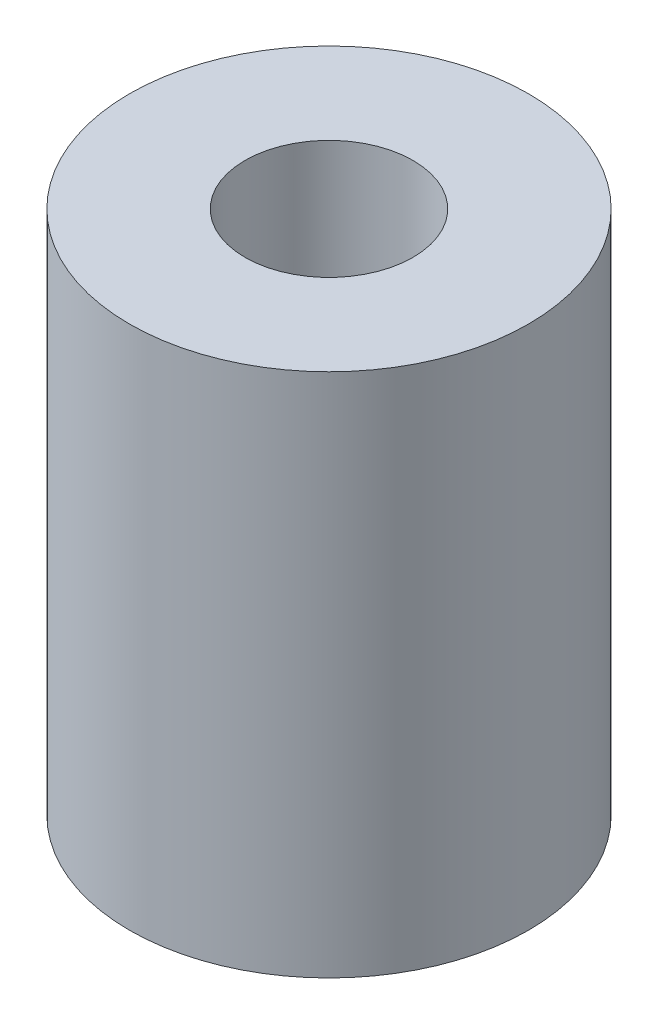
SolidWorks part; units mm, degrees
ref_plane "Alzado" through (0, 0, 0) normal (0, 0, 1) x (1, 0, 0)
ref_plane "Planta" through (0, 0, 0) normal (0, 1, 0) x (1, 0, 0)
ref_plane "Vista lateral" through (0, 0, 0) normal (1, 0, 0) x (0, 0, -1)
sketch "Croquis1" plane through (0, 0, 0) normal (0, 1, 0) x (1, 0, 0)
  circle A0 centre (0, 0) radius 9.5
  dimension "D1" = 19
extrude "Saliente-Extruir1" add sketch "Croquis1" along normal blind 25
sketch "Croquis2" plane through (0, 25, 0) normal (0, 1, 0) x (1, 0, 0)
  circle A0 centre (0, 0) radius 4
  dimension "D1" = 8
extrude "Cortar-Extruir1" cut sketch "Croquis2" against normal blind 17
sketch "Croquis3" plane through (0, 0, 0) normal (0, -1, 0) x (1, 0, 0)
  circle A0 centre (0, 0) radius 2.5
  dimension "D1" = 5
extrude "Cortar-Extruir2" cut sketch "Croquis3" against normal blind 8
